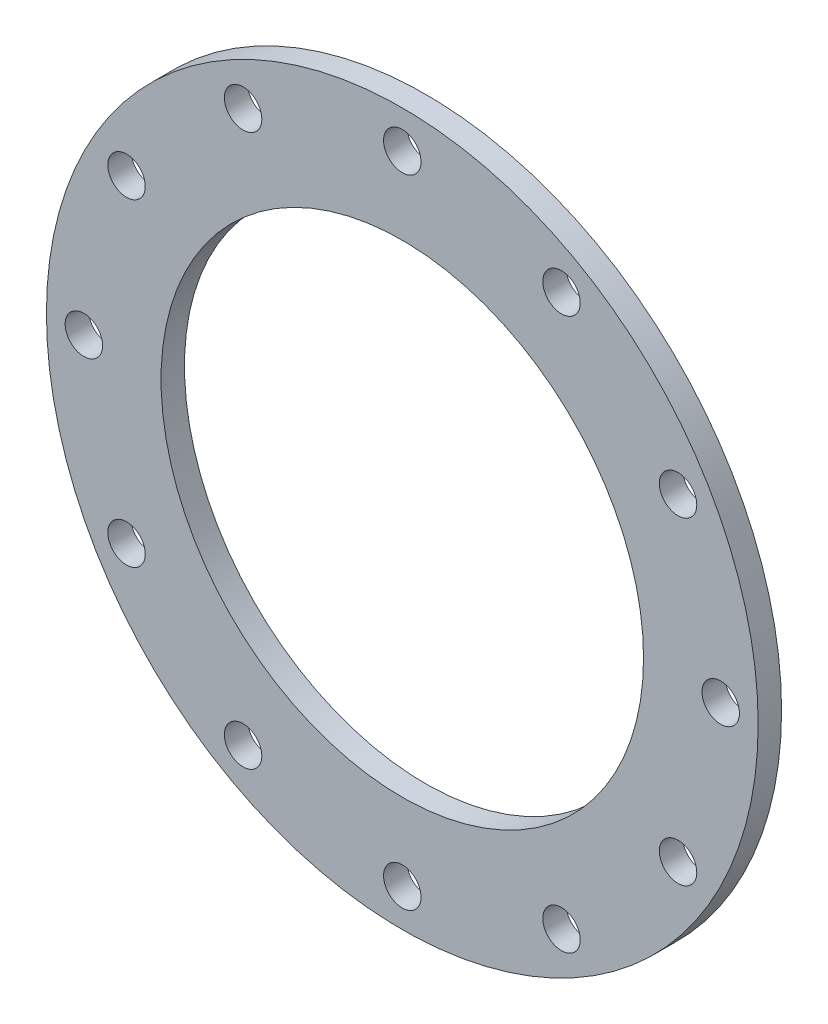
SolidWorks part; units mm, degrees
material "Ductile Iron"
ref_plane "Front Plane" through (0, 0, 0) normal (0, 0, 1) x (1, 0, 0)
ref_plane "Top Plane" through (0, 0, 0) normal (0, 1, 0) x (1, 0, 0)
ref_plane "Right Plane" through (0, 0, 0) normal (1, 0, 0) x (0, 0, -1)
sketch "Profile Sketch" plane through (0, 0, 0) normal (0, 0, 1) x (1, 0, 0)
  circle A0 centre (0, 0) radius 241.3
  circle A1 centre (0, 0) radius 163.576
  circle A2 centre (0, 0) radius 215.9 construction
  circle A3 centre (0, 215.9) radius 12.7 construction
  circle A4 centre (107.95, 186.9749) radius 12.7 construction
  circle A5 centre (186.9749, 107.95) radius 12.7 construction
  circle A6 centre (215.9, 0) radius 12.7 construction
  circle A7 centre (186.9749, -107.95) radius 12.7 construction
  circle A8 centre (107.95, -186.9749) radius 12.7 construction
  circle A9 centre (0, -215.9) radius 12.7 construction
  circle A10 centre (-107.95, -186.9749) radius 12.7 construction
  circle A11 centre (-186.9749, -107.95) radius 12.7 construction
  circle A12 centre (-215.9, 0) radius 12.7 construction
  circle A13 centre (-186.9749, 107.95) radius 12.7 construction
  circle A14 centre (-107.95, 186.9749) radius 12.7 construction
  point P31 (0, 0)
  dimension "D1" = 327.152
  dimension "D2" = 482.6
  dimension "D3" = 431.8
  dimension "D4" = 25.4
  dimension "D5" = 12
extrude "Boss-Extrude1" add sketch "Profile Sketch" along normal mid plane 15.875 contours A0 | A1
hole_wizard "1 (1) Diameter Hole1" positions "3DSketch1" profile "Sketch1" hole size "1" standard "ANSI Inch" end condition through all
sketch3d "3DSketch1"
  point P0 (215.9, 0, 7.9375)
sketch "Sketch1" plane through (215.9, 0, 7.9375) normal (1, 0, 0) x (0, -1, 0)
  line L0 (0, 0) -> (0, 15.875)
  line L1 (0, 15.875) -> (12.7, 15.875)
  line L2 (12.7, 15.875) -> (12.7, 0)
  line L5 (12.7, 0) -> (0, 0)
  line L11 (0, -6.35) -> (0, 107.95) construction
  dimension "Thru Hole Dia." = 25.4
  dimension "Thru Hole Depth" = 15.875
pattern_circular "CirPattern1" count 12 over 360 about axis through (0, 0, 0) along (0, 0, 1) of "1 (1) Diameter Hole1"
equation "\"ID\"= 12.88in'RJSALES"
equation "\"BC\"= 17in'RJSALES"
equation "\"OD\"= 19in'RJSALES"
equation "\"HD\"= 1in'RJSALES"
equation "\"T\"= 0.625in'RJSALES"
equation "\"D1@Profile Sketch\" = \"ID\""
equation "\"D2@Profile Sketch\" = \"OD\""
equation "\"D3@Profile Sketch\" = \"BC\""
equation "\"D4@Profile Sketch\" = \"HD\""
equation "\"D1@Boss-Extrude1\"=\"T\""
